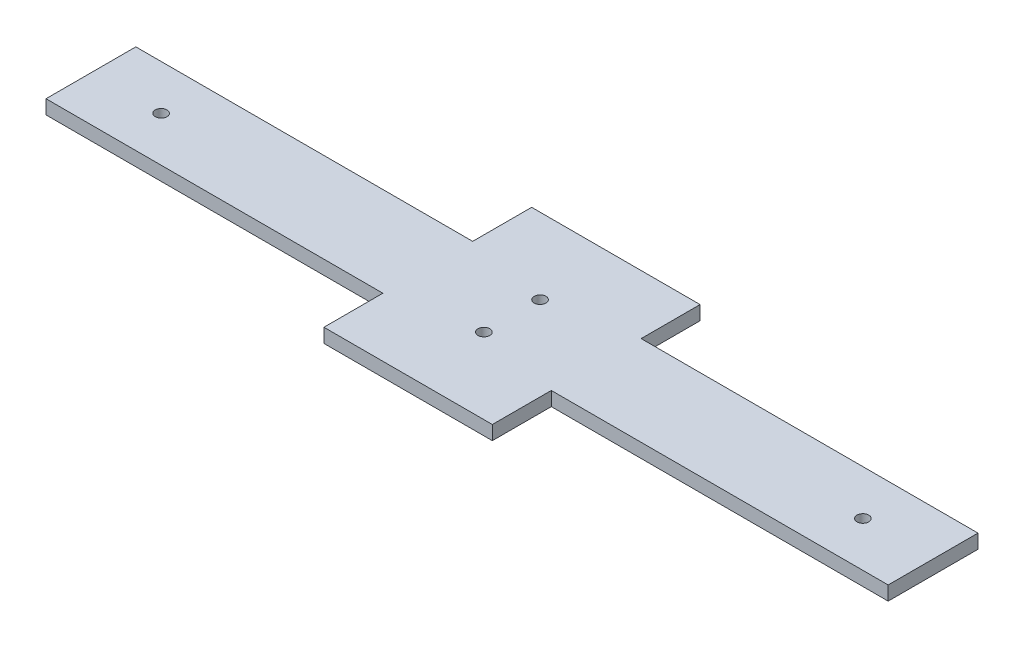
SolidWorks part; units mm, degrees
ref_plane "前视基准面" through (0, 0, 0) normal (0, 0, 1) x (1, 0, 0)
ref_plane "上视基准面" through (0, 0, 0) normal (0, 1, 0) x (1, 0, 0)
ref_plane "右视基准面" through (0, 0, 0) normal (1, 0, 0) x (0, 0, -1)
sketch "草图1" plane through (0, 0, 0) normal (0, 1, 0) x (1, 0, 0)
  line L0 (-180, 180) -> (-180, 103)
  line L1 (-210, -180) -> (-180, -180)
  line L2 (-210, -180) -> (-210, 180)
  line L3 (-210, 180) -> (-180, 180)
  line L4 (210, -180) -> (210, 180)
  line L5 (-210, -180) -> (210, 180) construction
  line L6 (-210, 180) -> (210, -180) construction
  line L7 (-180, 103) -> (-80, 103)
  line L8 (-80, 103) -> (-80, 180)
  line L9 (180, 180) -> (210, 180)
  line L10 (0, -14) -> (0, 14) construction
  line L11 (-210, 0) -> (210, 0) construction
  line L12 (-180, -180) -> (-180, -103)
  line L13 (-180, -103) -> (-80, -103)
  line L14 (-80, -103) -> (-80, -180)
  line L15 (80, -103) -> (80, -180)
  line L16 (180, -180) -> (180, -103)
  line L17 (180, -103) -> (80, -103)
  line L18 (180, 180) -> (180, 103)
  line L19 (180, 103) -> (80, 103)
  line L20 (80, 103) -> (80, 180)
  line L21 (-80, 180) -> (80, 180)
  line L22 (-80, -180) -> (80, -180)
  line L23 (180, -180) -> (210, -180)
  point P0 (0, 0)
  dimension "D1" = 420
  dimension "D2" = 360
  dimension "D3" = 100
  dimension "D4" = 77
  dimension "D5" = 30
extrude "凸台-拉伸1" add sketch "草图1" along normal blind 5
sketch "草图2" plane through (0, 5, 0) normal (0, 1, 0) x (1, 0, 0)
  line L0 (130, -103) -> (130, -89.161) construction
  line L1 (80, -103) -> (180, -103) construction
  line L2 (145, -88.5) -> (115, -88.5) construction
  line L3 (0, -180) -> (0, 180) construction
  line L4 (-80, -180) -> (80, -180) construction
  line L5 (80, 180) -> (-80, 180) construction
  line L6 (210, 0) -> (-210, 0) construction
  line L7 (210, -180) -> (210, 180) construction
  line L8 (-210, 180) -> (-210, -180) construction
  line L9 (145, 88.5) -> (115, 88.5) construction
  line L10 (130, 103) -> (130, 89.161) construction
  line L11 (-130, 103) -> (-130, 89.161) construction
  line L12 (-145, 88.5) -> (-115, 88.5) construction
  line L13 (-145, -88.5) -> (-115, -88.5) construction
  line L14 (-130, -103) -> (-130, -89.161) construction
  circle A0 centre (115, -88.5) radius 2.1
  circle A1 centre (145, -88.5) radius 2.1
  circle A2 centre (130, -95.5) radius 2.1
  circle A3 centre (130, 95.5) radius 2.1
  circle A4 centre (145, 88.5) radius 2.1
  circle A5 centre (115, 88.5) radius 2.1
  circle A6 centre (-115, 88.5) radius 2.1
  circle A7 centre (-145, 88.5) radius 2.1
  circle A8 centre (-130, 95.5) radius 2.1
  circle A9 centre (-130, -95.5) radius 2.1
  circle A10 centre (-145, -88.5) radius 2.1
  circle A11 centre (-115, -88.5) radius 2.1
  point P10 (130, -88.5)
  dimension "D1" = 4.2
  dimension "D2" = 30
  dimension "D3" = 7
  dimension "D4" = 7.5
extrude "切除-拉伸1" cut sketch "草图2" against normal through all
fillet "圆角1" radius 5 8 edges at (-180, 2.5, -180) (180, 2.5, 180) (80, 2.5, 180) (-180, 2.5, 180) (-80, 2.5, 180) (-80, 2.5, -180) (180, 2.5, -180) (80, 2.5, -180)
sketch "草图3" plane through (0, 0, 0) normal (0, -1, 0) x (1, 0, 0)
  line L0 (84.75, 31.75) -> (84.75, -31.75) construction
  line L2 (80, 175) -> (80, 103) construction
  line L3 (80, 103) -> (80, -103) construction
  line L4 (80, 0) -> (210, 0) construction
  line L5 (210, 180) -> (210, -180) construction
  line L6 (171.25, 31.75) -> (171.25, -31.75) construction
  line L7 (171.25, 31.75) -> (84.75, 31.75) construction
  line L8 (171.25, -31.75) -> (84.75, -31.75) construction
  line L9 (0, 180) -> (0, -180) construction
  line L10 (-75, 180) -> (75, 180) construction
  line L11 (75, -180) -> (-75, -180) construction
  line L12 (-171.25, -31.75) -> (-84.75, -31.75) construction
  line L13 (-171.25, 31.75) -> (-84.75, 31.75) construction
  line L14 (-171.25, 31.75) -> (-171.25, -31.75) construction
  line L15 (-84.75, 31.75) -> (-84.75, -31.75) construction
  circle A0 centre (84.75, 31.75) radius 2.5
  circle A1 centre (84.75, -31.75) radius 2.5
  circle A2 centre (171.25, 31.75) radius 2.5
  circle A3 centre (171.25, -31.75) radius 2.5
  circle A4 centre (-171.25, -31.75) radius 2.5
  circle A5 centre (-171.25, 31.75) radius 2.5
  circle A6 centre (-84.75, -31.75) radius 2.5
  circle A7 centre (-84.75, 31.75) radius 2.5
  point P8 (84.75, 0)
  dimension "D1" = 63.5
  dimension "D2" = 5
  dimension "D3" = 5
  dimension "D5" = 5
  dimension "D6" = 86.5
  dimension "D7" = 5
  dimension "D4" = 4.75
extrude "切除-拉伸2" cut sketch "草图3" against normal through all
sketch "草图4" plane through (0, 0, 0) normal (0, -1, 0) x (1, 0, 0)
  line L0 (-125, 0) -> (125, 0) construction
  line L1 (0, 10) -> (0, -10) construction
  circle A0 centre (-125, 0) radius 2.1
  circle A1 centre (125, 0) radius 2.1
  circle A2 centre (0, 10) radius 2.1
  circle A3 centre (0, -10) radius 2.1
  dimension "D1" = 4.2
  dimension "D2" = 4.2
  dimension "D3" = 125
  dimension "D4" = 125
  dimension "D5" = 4.2
  dimension "D6" = 4.2
  dimension "D7" = 10
  dimension "D8" = 10
extrude "切除-拉伸3" cut sketch "草图4" against normal through all
sketch "草图5" plane through (0, 0, 0) normal (0, -1, 0) x (1, 0, 0)
  line L0 (-150, 16) -> (-150, -16)
  line L1 (-150, -16) -> (-30, -16)
  line L2 (150, -16) -> (150, 16)
  line L3 (-150, 16) -> (-30, 16)
  line L4 (30, 37) -> (30, 16)
  line L5 (30, -37) -> (-30, -37)
  line L6 (-30, -37) -> (-30, -16)
  line L7 (-30, 37) -> (30, 37)
  line L8 (30, -16) -> (30, -37)
  line L9 (30, 16) -> (150, 16)
  line L10 (30, -16) -> (150, -16)
  line L11 (-30, 16) -> (-30, 37)
  dimension "D1" = 32
  dimension "D2" = 16
  dimension "D3" = 300
  dimension "D4" = 150
  dimension "D5" = 74
  dimension "D6" = 37
  dimension "D7" = 60
  dimension "D8" = 30
extrude "切除-拉伸4" cut sketch "草图5" against normal through all flip side to cut
